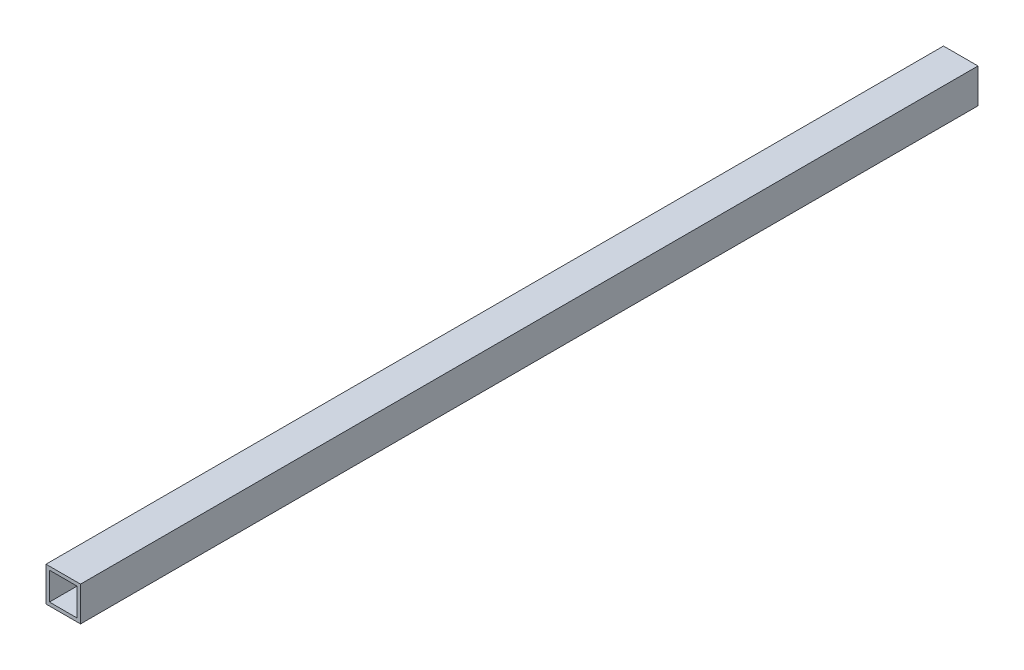
SolidWorks part; units mm, degrees
ref_plane "正面" through (0, 0, 0) normal (0, 0, 1) x (1, 0, 0)
ref_plane "平面" through (0, 0, 0) normal (0, 1, 0) x (1, 0, 0)
ref_plane "右側面" through (0, 0, 0) normal (1, 0, 0) x (0, 0, -1)
sketch "ｽｹｯﾁ3" plane through (0, 0, 0) normal (0, 0, 1) x (1, 0, 0)
  line L1 (-10, 10) -> (10, 10)
  line L2 (-10, 10) -> (-10, -10)
  line L3 (-10, -10) -> (10, -10)
  line L4 (10, 10) -> (10, -10)
  line L5 (-10, 10) -> (10, -10) construction
  line L6 (-10, -10) -> (10, 10) construction
  point P0 (0, 0)
  dimension "D1" = 20
  dimension "D2" = 20
extrude "ﾎﾞｽ - 押し出し1" add sketch "ｽｹｯﾁ3" along normal blind 500
sketch "ｽｹｯﾁ4" plane through (10, 0, 0) normal (1, 0, 0) x (0, 0, -1)
  line L1 (-500, 10) -> (-490, 10)
  line L2 (-500, 10) -> (-500, 0)
  line L3 (-500, 0) -> (-490, 0)
  line L4 (-490, 10) -> (-490, 0)
  line L5 (-500, -10) -> (-490, -10)
  line L6 (-500, -10) -> (-500, 0)
  line L7 (-500, 0) -> (-490, 0)
  line L8 (-490, -10) -> (-490, 0)
  line L9 (0, 10) -> (-10, 10)
  line L10 (0, 10) -> (0, 0)
  line L11 (0, 0) -> (-10, 0)
  line L12 (-10, 10) -> (-10, 0)
  line L13 (0, -10) -> (-10, -10)
  line L14 (0, -10) -> (0, 0)
  line L15 (0, 0) -> (-10, 0)
  line L16 (-10, -10) -> (-10, 0)
  circle A0 centre (-490, 0) radius 2.2
  circle A1 centre (-490, 0) radius 5.5
  circle A2 centre (-10, 0) radius 5.5
  circle A3 centre (-10, 0) radius 2.2
  dimension "D9" = 11
  dimension "D10" = 4.4
  dimension "D11" = 11
  dimension "D12" = 4.4
  dimension "D1" = 10
  dimension "D2" = 10
  dimension "D3" = 10
  dimension "D4" = 10
  dimension "D5" = 10
  dimension "D6" = 10
  dimension "D7" = 10
  dimension "D8" = 10
sketch "ｽｹｯﾁ5" plane through (0, 10, 0) normal (0, 1, 0) x (1, 0, 0)
  line L0 (0, -500) -> (0, -470)
  line L1 (10, -500) -> (-10, -500) construction
  line L2 (0, -470) -> (0, 30)
  circle A0 centre (0, -470) radius 2.2
  circle A1 centre (0, 30) radius 2.2
  dimension "D2" = 4.4
  dimension "D4" = 4.4
  dimension "D1" = 30
  dimension "D3" = 500
sketch "ｽｹｯﾁ6" plane through (0, 0, 500) normal (0, 0, 1) x (1, 0, 0)
  line L1 (-8, 8) -> (8, 8)
  line L2 (-8, 8) -> (-8, -8)
  line L3 (-8, -8) -> (8, -8)
  line L4 (8, 8) -> (8, -8)
  line L5 (-8, 8) -> (8, -8) construction
  line L6 (-8, -8) -> (8, 8) construction
  point P0 (0, 0)
  dimension "D1" = 16
  dimension "D2" = 16
extrude "ｶｯﾄ - 押し出し3" cut sketch "ｽｹｯﾁ6" against normal blind 560 contours L2 L1 L4 L3
sketch "ｽｹｯﾁ7" plane through (0, 0, 0) normal (0, 0, -1) x (-1, 0, 0)
  line L0 (10, 10) -> (10, -10) construction
  line L1 (-10, 20) -> (10, 20)
  line L2 (-10, 20) -> (-10, -20)
  line L3 (-10, -20) -> (10, -20)
  line L4 (10, 20) -> (10, -20)
  line L5 (-10, 20) -> (10, -20) construction
  line L6 (-10, -20) -> (10, 20) construction
  line L7 (8, -8) -> (-8, -8) construction
  line L8 (-8, 8) -> (8, 8)
  line L9 (-8, 8) -> (-8, -8)
  line L10 (-8, -8) -> (8, -8)
  line L11 (8, 8) -> (8, -8)
  line L12 (-8, 8) -> (8, -8) construction
  line L13 (-8, -8) -> (8, 8) construction
  line L14 (8, 8) -> (8, -8) construction
  point P0 (0, 0)
  point P8 (0, 0)
sketch "ｽｹｯﾁ8" plane through (0, 0, 500) normal (0, 0, 1) x (1, 0, 0)
  line L1 (-10, 10) -> (10, 10)
  line L2 (-10, 10) -> (-10, -10)
  line L3 (-10, -10) -> (10, -10)
  line L4 (10, 10) -> (10, -10)
  line L5 (-10, 10) -> (10, -10) construction
  line L6 (-10, -10) -> (10, 10) construction
  line L7 (-8, 8) -> (8, 8)
  line L8 (-8, 8) -> (-8, -8)
  line L9 (-8, -8) -> (8, -8)
  line L10 (8, 8) -> (8, -8)
  line L11 (-8, 8) -> (8, -8) construction
  line L12 (-8, -8) -> (8, 8) construction
  point P0 (0, 0)
  point P7 (0, 0)
extrude "ﾎﾞｽ - 押し出し3" add sketch "ｽｹｯﾁ8" along normal blind 20
sketch "ｽｹｯﾁ9" plane through (0, 10, 0) normal (0, 1, 0) x (1, 0, 0)
  line L0 (0, -520) -> (0, -510)
  line L1 (10, -520) -> (-10, -520) construction
  circle A0 centre (0, -510) radius 2.2
  dimension "D2" = 4.4
  dimension "D1" = 10
sketch "ｽｹｯﾁ11" plane through (0, -10, 0) normal (0, -1, 0) x (-1, 0, 0)
  line L0 (0, 0) -> (0, -30)
  line L1 (0, -520) -> (0, -490)
  line L2 (10, -520) -> (-10, -520) construction
  circle A0 centre (0, -30) radius 2.1
  circle A1 centre (0, -490) radius 2.1
  dimension "D2" = 4.2
  dimension "D4" = 4.2
  dimension "D1" = 30
  dimension "D3" = 30
sketch "ｽｹｯﾁ12" plane through (-10, 0, 0) normal (-1, 0, 0) x (0, 0, 1)
  line L0 (0, 0) -> (20, 0)
  line L1 (0, 10) -> (0, -10) construction
  line L2 (520, 0) -> (500, 0)
  line L3 (520, 10) -> (520, -10) construction
  circle A0 centre (20, 0) radius 1
  circle A1 centre (500, 0) radius 1
  dimension "D2" = 2
  dimension "D4" = 2
  dimension "D1" = 20
  dimension "D3" = 20
extrude "ｶｯﾄ - 押し出し7" cut sketch "ｽｹｯﾁ12" against normal blind 10
hole_wizard "M4x0.7 ねじ穴1" positions "3Dｽｹｯﾁ1" profile "ｽｹｯﾁ13" tap size "M4x0.7" standard "JIS"
sketch3d "3Dｽｹｯﾁ1"
  line L0 (-8, 0, 20) -> (-10, 0, 20) construction
  line L1 (-8, 0, 500) -> (-10, 0, 500) construction
  point P0 (-10, 0, 20)
  point P4 (-8, 0, 500)
sketch "ｽｹｯﾁ13" plane through (-10, 0, 20) normal (0, 1, 0) x (0, 0, 1)
  line L0 (0, 0) -> (0, 12.4914)
  line L1 (0, 12.4914) -> (1.65, 11.5)
  line L2 (1.65, 11.5) -> (1.65, 0)
  line L5 (1.65, 0) -> (0, 0)
  line L10 (0, 12.4914) -> (-1.65, 11.5) construction
  line L11 (0, -6.35) -> (0, 107.95) construction
  dimension "ねじ下穴ﾄﾞﾘﾙ直径" = 3.3
  dimension "ねじ下穴ﾄﾞﾘﾙの深さ" = 11.5
  dimension "ﾄﾞﾘﾙ角度" = 118
cosmetic thread "穴のねじ山1" parameters "D1"=2, "D2"=4
cosmetic thread "穴のねじ山2" parameters "D1"=2, "D2"=4
